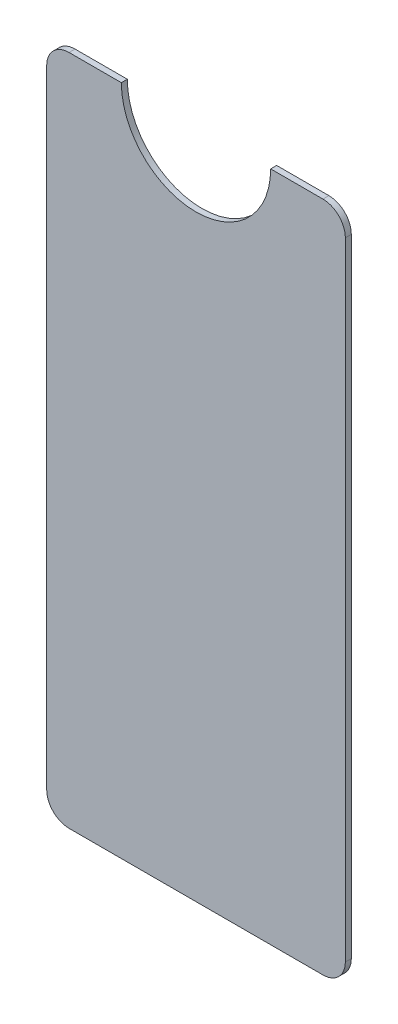
SolidWorks part; units mm, degrees
ref_plane "Front Plane" through (0, 0, 0) normal (0, 0, 1) x (1, 0, 0)
ref_plane "Top Plane" through (0, 0, 0) normal (0, 1, 0) x (1, 0, 0)
ref_plane "Right Plane" through (0, 0, 0) normal (1, 0, 0) x (0, 0, -1)
sketch "Sketch1" plane through (0, 0, 0) normal (0, 0, 1) x (1, 0, 0)
  line L0 (30, 90) -> (37, 90)
  line L1 (3, 0) -> (37, 0)
  line L2 (0, 3) -> (0, 87)
  line L3 (3, 90) -> (10, 90)
  line L4 (40, 3) -> (40, 87)
  arc A0 (10, 90) -> (30, 90) centre (20, 90) ccw
  arc A1 (0, 87) -> (3, 90) centre (3, 87) cw
  arc A2 (40, 87) -> (37, 90) centre (37, 87) ccw
  arc A3 (0, 3) -> (3, 0) centre (3, 3) ccw
  arc A4 (37, 0) -> (40, 3) centre (37, 3) ccw
  point P8 (0, 0)
  point P9 (0, 0)
  point P12 (0, 90)
  point P17 (0, 0)
  point P20 (40, 0)
  dimension "D3" = 10
  dimension "D5" = 3
  dimension "D6" = 3
  dimension "D7" = 3
  dimension "D8" = 3
  dimension "D1" = 40
  dimension "D2" = 90
  dimension "D4" = 20
extrude "Boss-Extrude1" add sketch "Sketch1" along normal blind 0.8
